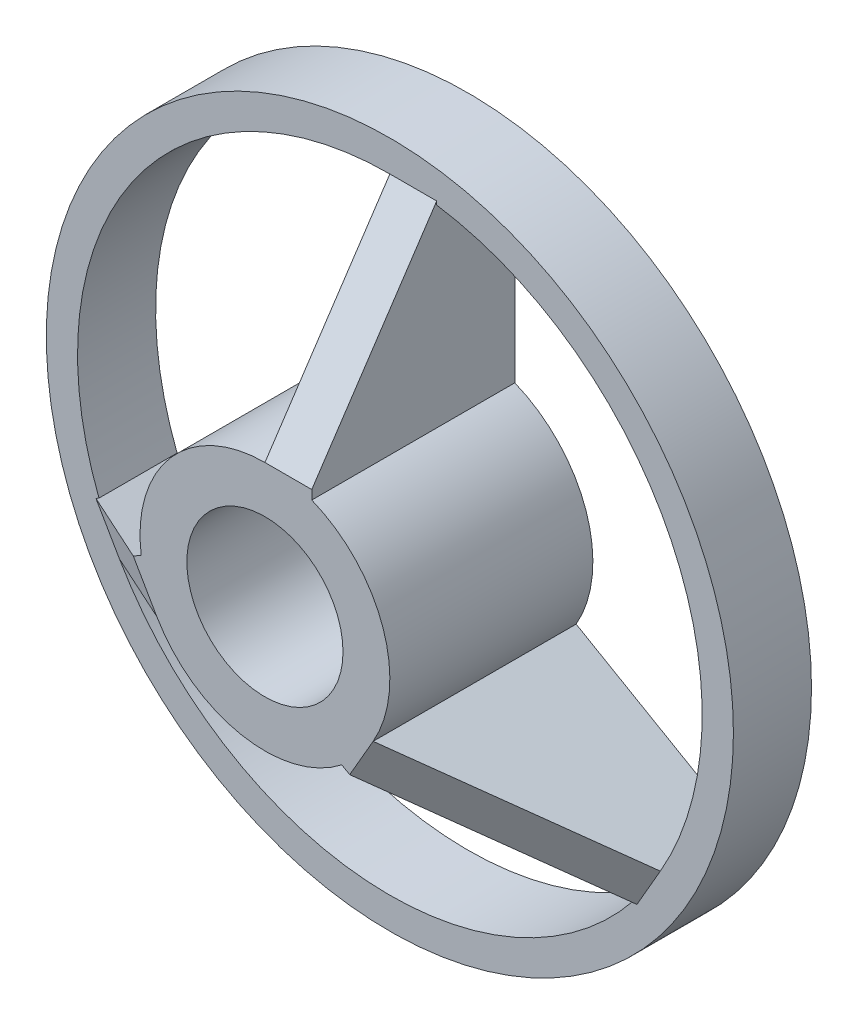
SolidWorks part; units mm, degrees
ref_plane "Front Plane" through (0, 0, 0) normal (0, 0, 1) x (1, 0, 0)
ref_plane "Top Plane" through (0, 0, 0) normal (0, 1, 0) x (1, 0, 0)
ref_plane "Right Plane" through (0, 0, 0) normal (1, 0, 0) x (0, 0, -1)
sketch "Sketch7" plane through (0, 0, 0) normal (0, 0, 1) x (1, 0, 0)
  circle A0 centre (0, 0) radius 20
  circle A1 centre (0, 0) radius 22
  dimension "D1" = 40
  dimension "D2" = 2
extrude "Boss-Extrude7" add sketch "Sketch7" along normal blind 5
sketch "Sketch8" plane through (0, 0, 0) normal (0, 0, 1) x (1, 0, 0)
  circle A0 centre (0, 0) radius 5
  circle A1 centre (0, 0) radius 8
  dimension "D1" = 10
  dimension "D2" = 3
extrude "Boss-Extrude8" add sketch "Sketch8" along normal blind 13 separate body
sketch "Sketch9" plane through (0, 0, 0) normal (1, 0, 0) x (0, 0, -1)
  line L0 (0, 8) -> (-13, 8) construction
  line L1 (0, -20) -> (0, 20) construction
  line L2 (0, -8) -> (0, 8) construction
  line L3 (-13, 8) -> (-13, -8) construction
  line L4 (-13, 8) -> (-5, 20)
  line L5 (-5, 20) -> (-5, -20) construction
  line L6 (-5, 22) -> (-5, -22) construction
  line L7 (-5, 20) -> (0, 20)
  line L8 (0, 20) -> (0, 8)
  line L9 (-13, 8) -> (-13, 5)
  line L10 (-13, 5) -> (-13, -5) construction
  line L11 (-13, 5) -> (0, 5)
  line L12 (0, -5) -> (0, 5) construction
  line L13 (0, 5) -> (0, 8)
extrude "Boss-Extrude10" add sketch "Sketch9" along normal blind 3
pattern_circular "CirPattern2" count 3 over 360 about axis through (0, 0, 0) along (0, 0, 1) of "Boss-Extrude10"
